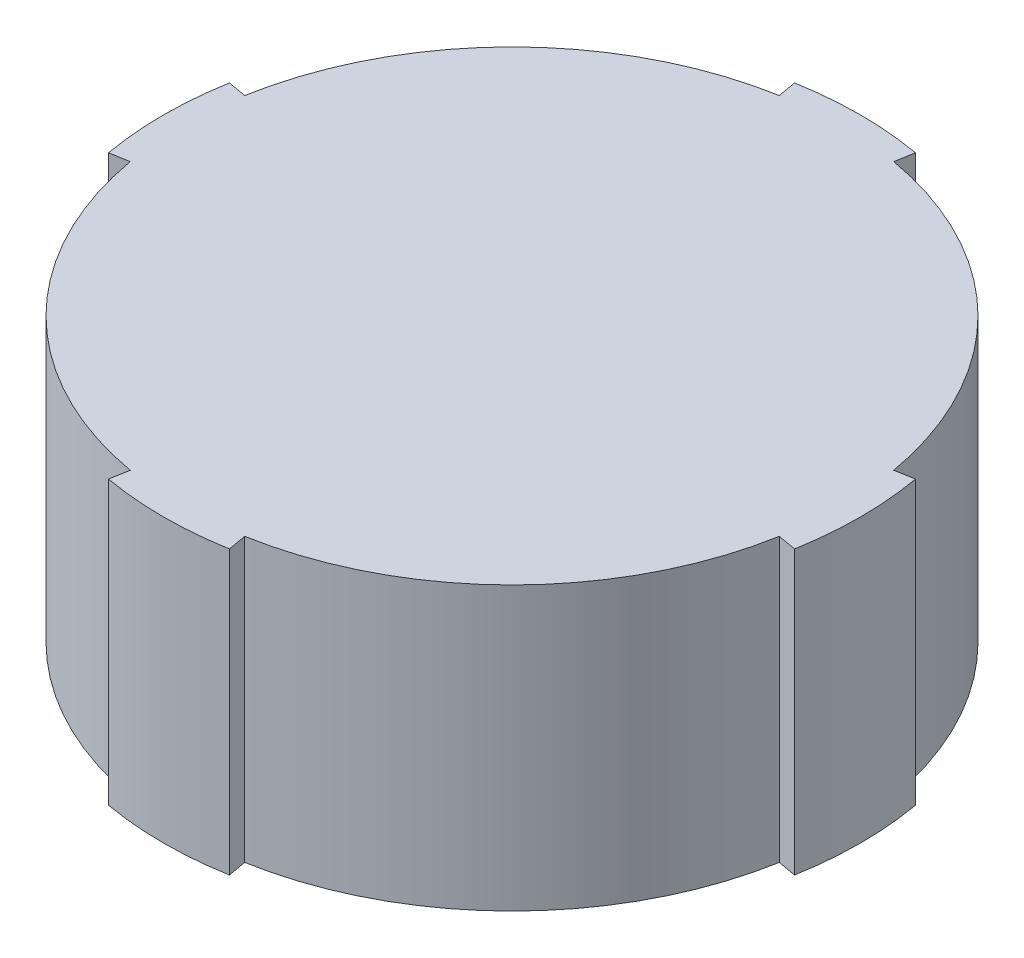
SolidWorks part; units mm, degrees
ref_plane "Front Plane" through (0, 0, 0) normal (0, 0, 1) x (1, 0, 0)
ref_plane "Top Plane" through (0, 0, 0) normal (0, 1, 0) x (1, 0, 0)
ref_plane "Right Plane" through (0, 0, 0) normal (1, 0, 0) x (0, 0, -1)
sketch "Sketch1" plane through (0, 0, 0) normal (0, 1, 0) x (1, 0, 0)
  circle A0 centre (0, 0) radius 37
  dimension "D1" = 74
extrude "Boss-Extrude1" add sketch "Sketch1" along normal blind 30
sketch "Sketch2" plane through (0, 30, 0) normal (0, 1, 0) x (1, 0, 0)
  line L0 (0, 0) -> (0, 37)
  line L1 (0, 0) -> (37, 0)
  line L2 (0, 0) -> (6.425, 36.4379)
  line L3 (0, 0) -> (36.4379, 6.425)
  line L4 (0, 0) -> (37, 0)
  line L5 (0, 0) -> (36.4379, -6.425)
  line L6 (0, 0) -> (0, -37)
  line L7 (0, 0) -> (-6.425, -36.4379)
  line L8 (0, 0) -> (-37, 0)
  line L9 (0, 0) -> (-36.4379, 6.425)
  line L10 (0, 0) -> (6.425, -36.4379)
  line L11 (0, 0) -> (-36.4379, -6.425)
  line L12 (0, 0) -> (-6.425, 36.4379)
  circle A0 centre (0, 0) radius 37 construction
  circle A1 centre (0, 0) radius 37
  circle A2 centre (0, 0) radius 35
  point P20 (0, 0)
  point P23 (0, 0)
  circle M7 centre (0, 0) radius 37
  dimension "D1" = 10
  dimension "D5" = 70
  dimension "D2" = 10
  dimension "D3" = 4
  dimension "D4" = 4
extrude "Cut-Extrude1" cut sketch "Sketch2" against normal blind 30 contours A2 L3 L2 M7 | A2 L12 L9 M7 | A2 L11 L7 M7 | A2 L10 L5 M7 | A1
